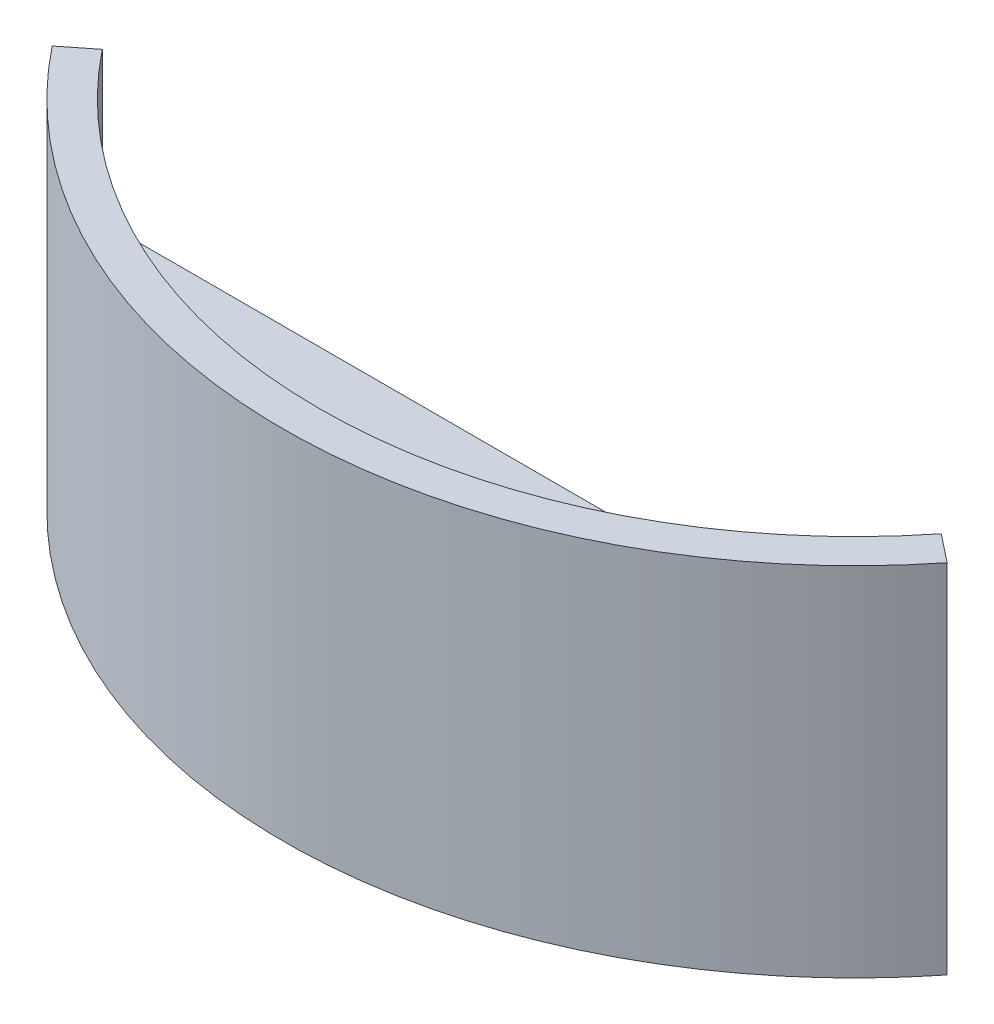
SolidWorks part; units mm, degrees
ref_plane "Front Plane" through (0, 0, 0) normal (0, 0, 1) x (1, 0, 0)
ref_plane "Top Plane" through (0, 0, 0) normal (0, 1, 0) x (1, 0, 0)
ref_plane "Right Plane" through (0, 0, 0) normal (1, 0, 0) x (0, 0, -1)
sketch "Sketch1" plane through (0, 0, 0) normal (0, 1, 0) x (1, 0, 0)
  line L0 (-25.0667, 10.1087) -> (-23.5, 11.3519)
  line L1 (23.5, 11.3519) -> (25.0667, 10.1087)
  arc A0 (-23.5, 11.3519) -> (23.5, 11.3519) centre (0, 30) ccw
  arc A1 (-25.0667, 10.1087) -> (25.0667, 10.1087) centre (0, 30) ccw
  dimension "D1" = 30
  dimension "D2" = 47
  dimension "D3" = 2
extrude "Boss-Extrude1" add sketch "Sketch1" along normal mid plane 20
sketch "Sketch2" plane through (0, 0, 0) normal (0, 1, 0) x (1, 0, 0)
  line L1 (-23.2164, 11) -> (23.2164, 11)
  arc A0 (-23.5, 11.3519) -> (23.5, 11.3519) centre (0, 30) ccw construction
  arc A1 (-23.2164, 11) -> (23.2164, 11) centre (0, 30) ccw
  point P7 (22.1029, 9.7155)
  dimension "D1" = 11
extrude "Boss-Extrude2" add sketch "Sketch2" along normal mid plane 4
